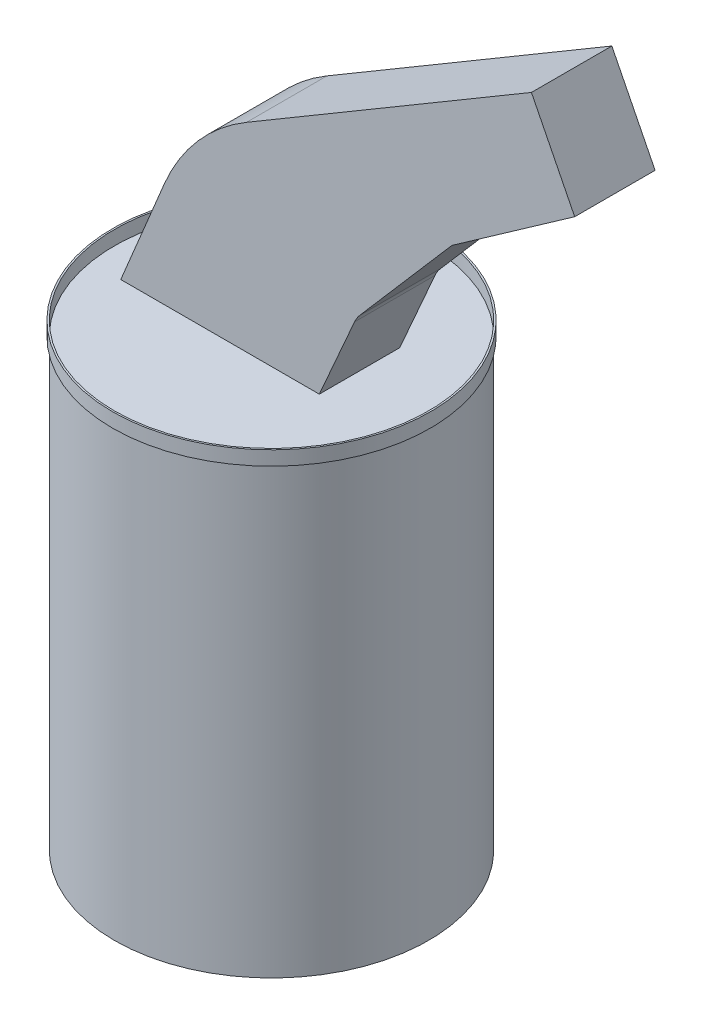
SolidWorks part; units mm, degrees
ref_plane "Front Plane" through (0, 0, 0) normal (0, 0, 1) x (1, 0, 0)
ref_plane "Top Plane" through (0, 0, 0) normal (0, 1, 0) x (1, 0, 0)
ref_plane "Right Plane" through (0, 0, 0) normal (1, 0, 0) x (0, 0, -1)
sketch "Sketch2" plane through (0, 0, 0) normal (0, 1, 0) x (1, 0, 0)
  circle A0 centre (0, 0) radius 47.5
  dimension "D1" = 95
extrude "Boss-Extrude1" add sketch "Sketch2" along normal mid plane 134.3
sketch "Sketch3" plane through (0, 67.15, 0) normal (0, 1, 0) x (1, 0, 0)
  circle A0 centre (0, 0) radius 48
  circle A1 centre (0, 0) radius 47.5 construction
  circle A2 centre (0, 0) radius 47.5
  dimension "D1" = 96
extrude "Boss-Extrude2" add sketch "Sketch3" along normal blind 4.3 separate body
sketch "Sketch4" plane through (0, 0, 0) normal (0, 0, 1) x (1, 0, 0)
  line L0 (103.7746, 156.4691) -> (90.7045, 182.4759)
  line L4 (66.654, 130.4098) -> (103.7746, 156.4691)
  line L6 (90.7045, 182.4759) -> (4.6081, 131.6092)
  line L7 (-20.2634, 103.0117) -> (-33.403, 71.45)
  line L8 (-33.403, 71.45) -> (26.597, 71.45)
  line L12 (66.654, 130.4098) -> (38.8362, 98.2173)
  line L13 (26.597, 71.45) -> (37.2467, 95.7)
  arc A0 (4.6081, 131.6092) -> (-20.2634, 103.0117) centre (35.1281, 79.9514) ccw
  arc A4 (37.2467, 95.7) -> (38.8362, 98.2173) centre (46.4027, 91.679) cw
extrude "Boss-Extrude3" add sketch "Sketch4" along normal mid plane 24.3 separate body
